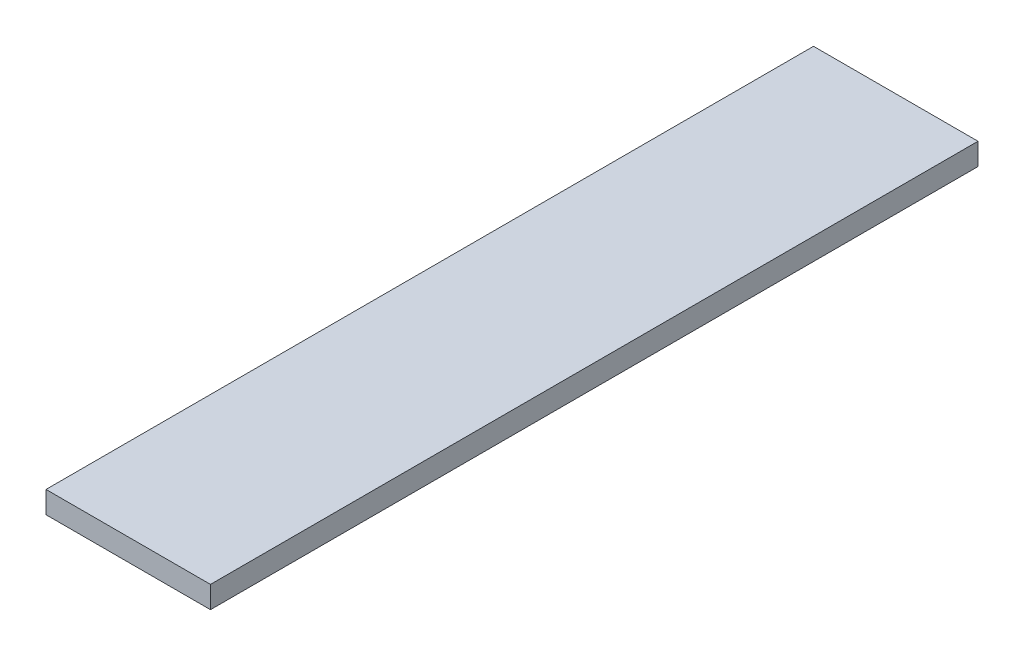
SolidWorks part; units mm, degrees
ref_plane "Front Plane" through (0, 0, 0) normal (0, 0, 1) x (1, 0, 0)
ref_plane "Top Plane" through (0, 0, 0) normal (0, 1, 0) x (1, 0, 0)
ref_plane "Right Plane" through (0, 0, 0) normal (1, 0, 0) x (0, 0, -1)
sketch "Sketch1" plane through (0, 0, 0) normal (0, 1, 0) x (1, 0, 0)
  line L1 (0, 0) -> (150, 0)
  line L2 (0, 0) -> (0, 700)
  line L3 (0, 700) -> (150, 700)
  line L4 (150, 0) -> (150, 700)
  dimension "D2" = 700
extrude "Boss-Extrude1" add sketch "Sketch1" along normal blind 20
